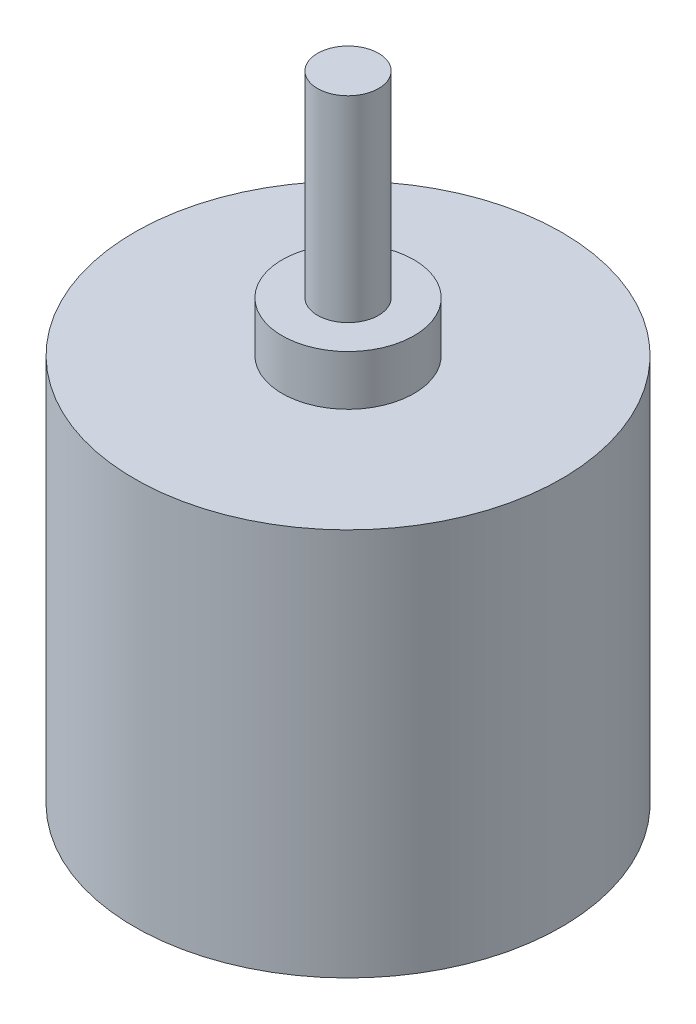
SolidWorks part; units mm, degrees
ref_plane "Front Plane" through (0, 0, 0) normal (0, 0, 1) x (1, 0, 0)
ref_plane "Top Plane" through (0, 0, 0) normal (0, 1, 0) x (1, 0, 0)
ref_plane "Right Plane" through (0, 0, 0) normal (1, 0, 0) x (0, 0, -1)
sketch "Sketch1" plane through (0, 0, 0) normal (0, 0, 1) x (1, 0, 0)
  line L0 (0, -45.7891) -> (0, 30.5578) construction
  line L1 (0, -26.75) -> (0, 26.75)
  line L2 (0, 26.75) -> (2.5, 26.75)
  line L3 (2.5, 26.75) -> (2.5, 10.65)
  line L4 (2.5, 10.65) -> (5.4, 10.65)
  line L5 (5.4, 10.65) -> (5.4, 6.55)
  line L6 (5.4, 6.55) -> (17.5, 6.55)
  line L7 (17.5, 6.55) -> (17.5, -25.25)
  line L9 (0, -26.75) -> (2.5, -26.75)
  line L10 (2.5, -26.75) -> (2.5, -25.25)
  line L11 (2.5, -25.25) -> (17.5, -25.25)
  dimension "D1" = 53.5
  dimension "D2" = 31.8
  dimension "D3" = 35.9
  dimension "D4" = 52
  dimension "D5" = 5
  dimension "D6" = 10.8
  dimension "D7" = 35
revolve "Revolve1" add sketch "Sketch1" angle 360 about L0
sketch "Sketch2" plane through (0, -25.25, 0) normal (0, -1, 0) x (1, 0, 0)
  line L0 (0, -9.25) -> (0, 9.25) construction
  line L1 (-12, 0) -> (12, 0) construction
  circle A0 centre (0, 9.25) radius 1.5
  circle A1 centre (12, 0) radius 1.5
  circle A2 centre (0, -9.25) radius 1.5
  circle A3 centre (-12, 0) radius 1.5
  point P9 (0, 8.7615)
  point P10 (14.2229, 0)
  dimension "D1" = 3
  dimension "D2" = 18.5
  dimension "D3" = 24
extrude "Cut-Extrude1" cut sketch "Sketch2" against normal blind 5
